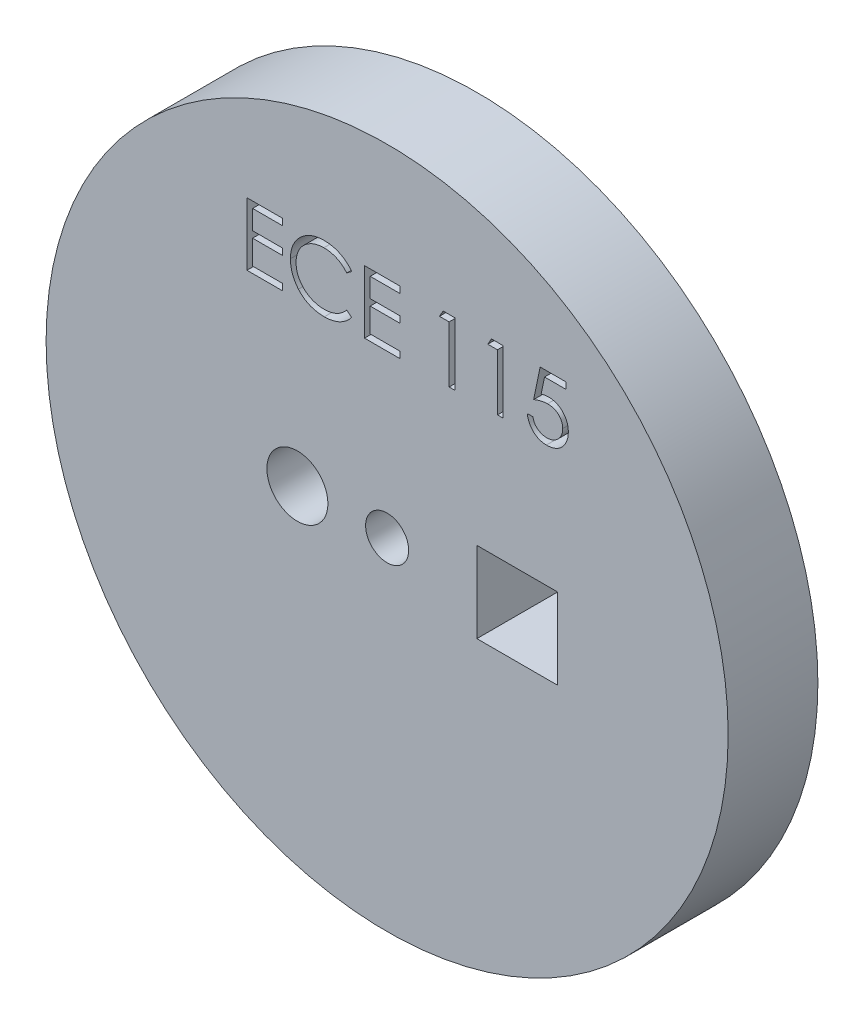
SolidWorks part; units mm, degrees
ref_plane "Front Plane" through (0, 0, 0) normal (0, 0, 1) x (1, 0, 0)
ref_plane "Top Plane" through (0, 0, 0) normal (0, 1, 0) x (1, 0, 0)
ref_plane "Right Plane" through (0, 0, 0) normal (1, 0, 0) x (0, 0, -1)
sketch "Sketch1" plane through (0, 0, 0) normal (0, 0, 1) x (1, 0, 0)
  circle A0 centre (0, 0) radius 19
  dimension "D1" = 38
extrude "Boss-Extrude1" add sketch "Sketch1" along normal blind 5
sketch "Sketch3" plane through (0, 0, 5) normal (0, 0, 1) x (1, 0, 0)
  line L0 (-19, 0) -> (19, 0) construction
  line L2 (5, 2.1402) -> (9.5, 2.1402)
  line L3 (5, 2.1402) -> (5, -2.3598)
  line L4 (5, -2.3598) -> (9.5, -2.3598)
  line L5 (9.5, 2.1402) -> (9.5, -2.3598)
  circle A0 centre (0, 0) radius 1.2
  circle A1 centre (0, 0) radius 19 construction
  circle A2 centre (-5, 0) radius 1.7
  dimension "D1" = 2.4
  dimension "D5" = 3.4
  dimension "D2" = 4.5
  dimension "D3" = 4.5
  dimension "D4" = 5
  dimension "D6" = 5
extrude "Cut-Extrude1" cut sketch "Sketch3" against normal blind 5
sketch "Sketch4" plane through (0, 0, 5) normal (0, 0, 1) x (1, 0, 0)
  text T0 "ECE 115"
extrude "Cut-Extrude2" cut sketch "Sketch4" against normal blind 5
